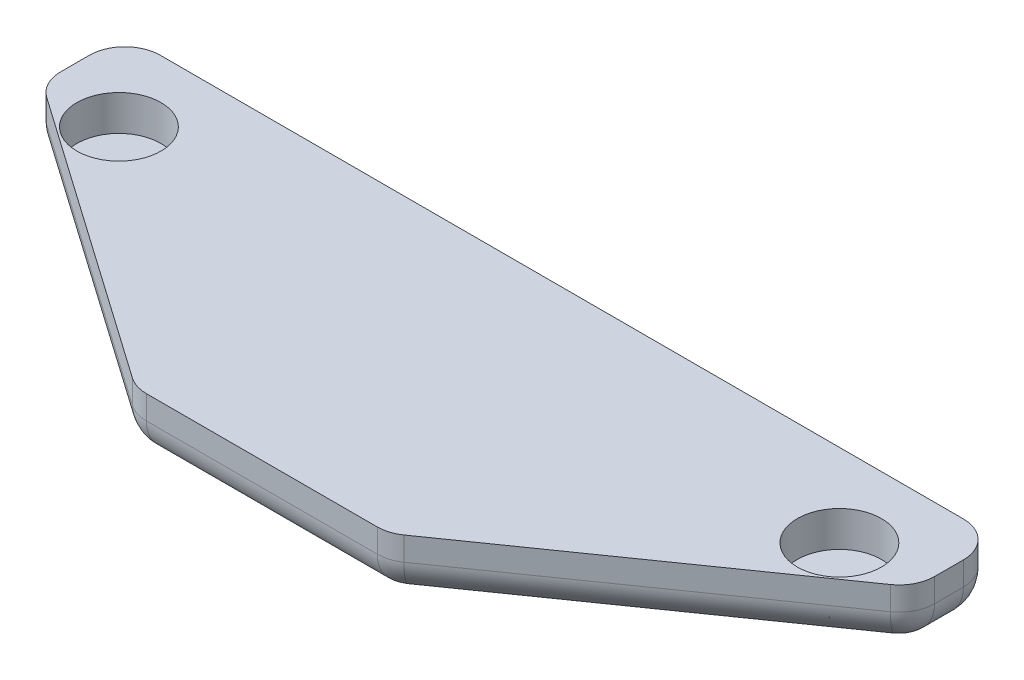
SolidWorks part; units mm, degrees
ref_plane "Front Plane" through (0, 0, 0) normal (0, 0, 1) x (1, 0, 0)
ref_plane "Top Plane" through (0, 0, 0) normal (0, 1, 0) x (1, 0, 0)
ref_plane "Right Plane" through (0, 0, 0) normal (1, 0, 0) x (0, 0, -1)
sketch "Sketch1" plane through (0, 0, 0) normal (0, 1, 0) x (1, 0, 0)
  line L0 (-21.2162, 11.7419) -> (-21.2162, 8.2419)
  line L1 (-21.2162, 8.2419) -> (-8.0762, -0.9581)
  line L2 (-8.0762, -0.9581) -> (-2.7162, -0.9581)
  line L7 (-2.7162, -0.9581) -> (-2.7162, 11.7419)
  line L10 (-2.7162, 11.7419) -> (-21.2162, 11.7419)
  dimension "D1" = 5.36
  dimension "D2" = 9.2
  dimension "D4" = 18.5
extrude "Boss-Extrude1" add sketch "Sketch1" along normal blind 2.5
sketch "Sketch2" plane through (0, 2.5, 0) normal (0, 1, 0) x (1, 0, 0)
  line L0 (-17.9662, 11.7419) -> (-17.9662, -0.786) construction
  line L1 (-2.7162, 11.7419) -> (-21.2162, 11.7419) construction
  line L2 (-21.2162, 8.2419) -> (-2.7162, 8.2419) construction
  line L3 (-21.2162, 11.7419) -> (-21.2162, 8.2419) construction
  line L4 (-2.7162, -0.9581) -> (-2.7162, 11.7419) construction
  circle A0 centre (-17.9662, 8.2419) radius 1.78
  dimension "D1" = 3.25
  dimension "D2" = 3.5
extrude "Cut-Extrude1" cut sketch "Sketch2" against normal blind 1.5
fillet "Fillet1" radius 1.5 7 edges at (-8.0762, 1.25, 0.9581) (-21.2162, 1.25, -8.2419) (-21.2162, 1.25, -11.7419) (-5.3962, 0, 0.9581) (-14.6462, 0, -3.6419) (-21.2162, 0, -9.9919) (-11.9662, 0, -11.7419)
mirror "Mirror1" about plane through (-2.7162, 2.5, 0.9581) normal (-1, 0, 0) of bodies 102
